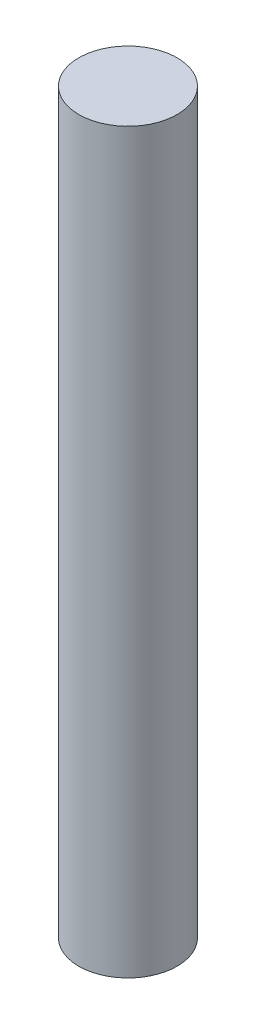
SolidWorks part; units mm, degrees
material "AISI 1020 Steel, Cold Rolled"
ref_plane "Front Plane" through (0, 0, 0) normal (0, 0, 1) x (1, 0, 0)
ref_plane "Top Plane" through (0, 0, 0) normal (0, 1, 0) x (1, 0, 0)
ref_plane "Right Plane" through (0, 0, 0) normal (1, 0, 0) x (0, 0, -1)
sketch "Sketch1" plane through (0, 0, 0) normal (0, 1, 0) x (1, 0, 0)
  circle A0 centre (0, 0) radius 5.08
  dimension "D1" = 10.16
extrude "Boss-Extrude1" add sketch "Sketch1" along normal blind 76.2 contours A0
